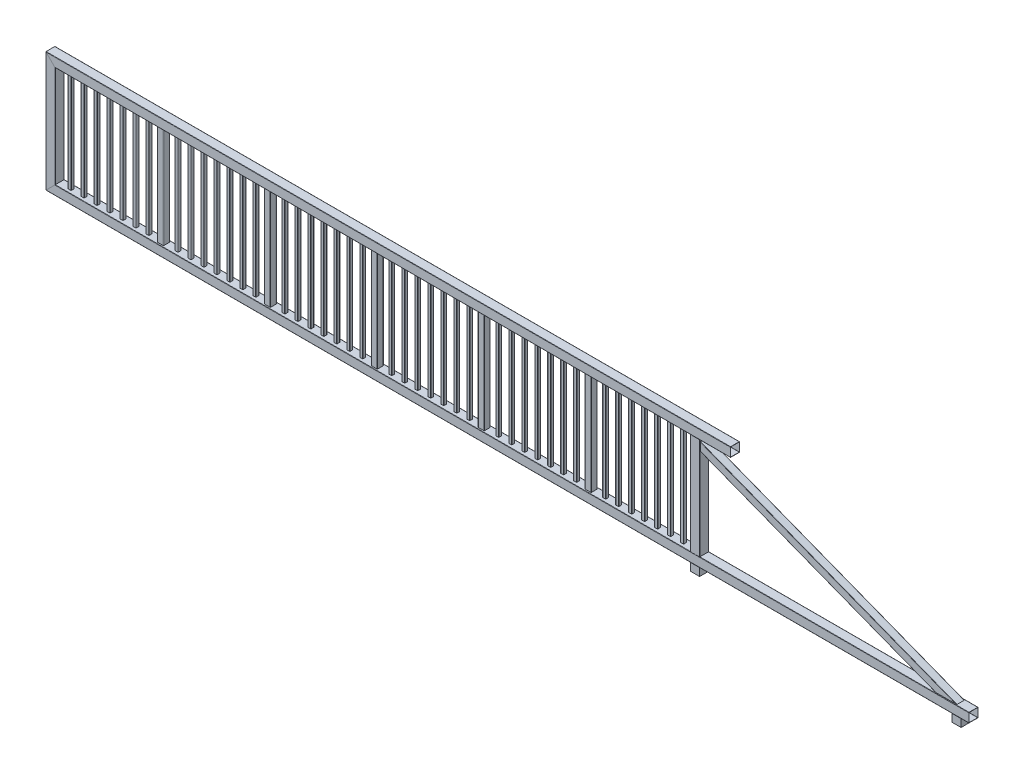
SolidWorks part; units mm, degrees
material "1.0037 (S235JR)"
ref_plane "Ebene vorne" through (0, 0, 0) normal (0, 0, 1) x (1, 0, 0)
ref_plane "Ebene oben" through (0, 0, 0) normal (0, 1, 0) x (1, 0, 0)
ref_plane "Ebene rechts" through (0, 0, 0) normal (1, 0, 0) x (0, 0, -1)
sketch "Skizze1" plane through (0, 0, 0) normal (0, 0, 1) x (1, 0, 0)
  line L0 (0, 0) -> (0, 1440)
  line L1 (0, 1440) -> (8840, 1440)
  line L2 (8380, 1320) -> (11790, 0)
  line L3 (11940, 0) -> (0, 0)
  line L4 (1410, 1440) -> (1410, 0)
  line L5 (2800, 1440) -> (2800, 0)
  line L6 (4190, 1440) -> (4190, 0)
  line L7 (5580, 1440) -> (5580, 0)
  line L8 (6970, 1440) -> (6970, 0)
  line L9 (5580, 1440) -> (5580, 0)
  line L10 (6970, 1440) -> (6970, 0)
  line L11 (1410, 864.301) -> (2800, 864.301) construction
  line L12 (2800, 864.301) -> (4190, 864.301) construction
  line L13 (4190, 864.301) -> (5580, 864.301) construction
  line L14 (5580, 864.301) -> (6970, 864.301) construction
  line L15 (6970, 864.301) -> (5580, 864.301) construction
  line L16 (5580, 864.301) -> (6970, 864.301) construction
  line L17 (8380, 1440) -> (8380, 0)
  line L18 (208.75, 1380) -> (208.75, 60)
  line L19 (60, 1380) -> (1370, 1380) construction
  line L20 (60, 1380) -> (60, 60) construction
  line L21 (60, 60) -> (1370, 60) construction
  line L22 (1370, 1380) -> (1370, 60) construction
  dimension "D1" = 8380
  dimension "D2" = 1440
  dimension "D3" = 460
  dimension "D4" = 1410
  dimension "D5" = 1390
  dimension "D6" = 11940
  dimension "D7" = 120
  dimension "D8" = 150
  dimension "D9" = 60
  dimension "D10" = 60
  dimension "D11" = 60
  dimension "D12" = 40
  dimension "D13" = 148.75
other "Strukturbauteil1"
ref_plane "Ebene1" through (0, 1440, 0) normal (1, 0, 0) x (0, 1, 0)
sketch "Skizze13" plane through (0, 1440, 0) normal (1, 0, 0) x (0, 1, 0)
  line L0 (57, -56) -> (57, 56)
  line L1 (56, -60) -> (-56, -60)
  line L2 (60, -56) -> (60, 56)
  line L3 (56, 60) -> (-56, 60)
  line L4 (-60, -56) -> (-60, 56)
  line L5 (56, 57) -> (-56, 57)
  line L6 (-57, -56) -> (-57, 56)
  line L7 (56, -57) -> (-56, -57)
  line L8 (0, -60) -> (0, 60) construction
  arc A0 (-60, 56) -> (-56, 60) centre (-56, 56) cw
  arc A1 (-56, -60) -> (-60, -56) centre (-56, -56) cw
  arc A2 (60, -56) -> (56, -60) centre (56, -56) cw
  arc A3 (56, 60) -> (60, 56) centre (56, 56) cw
  arc A4 (56, 57) -> (57, 56) centre (56, 56) cw
  arc A5 (-57, 56) -> (-56, 57) centre (-56, 56) cw
  arc A6 (-56, -57) -> (-57, -56) centre (-56, -56) cw
  arc A7 (57, -56) -> (56, -57) centre (56, -56) cw
  point P4 (0, 60)
  point P5 (0, -60)
  point P10 (-60, -60)
  point P13 (60, -60)
  point P16 (60, 60)
  point P25 (-60, -60)
  point P26 (-60, 60)
  point P27 (60, 60)
  point P30 (60, -60)
  point P31 (0, 0)
  point P32 (-60, 0)
  point P33 (60, 0)
  point P34 (0, 0)
  dimension "D3" = 4
  dimension "D1" = 120
  dimension "D2" = 120
  dimension "D4" = 3
other "Strukturbauteil2"
ref_plane "Ebene2" through (1410, 1440, 0) normal (0, -1, 0) x (1, 0, 0)
sketch "Skizze14" plane through (1410, 1440, 0) normal (0, -1, 0) x (1, 0, 0)
  line L0 (37, -36) -> (37, 36)
  line L1 (36, -40) -> (-36, -40)
  line L2 (40, -36) -> (40, 36)
  line L3 (36, 40) -> (-36, 40)
  line L4 (-40, -36) -> (-40, 36)
  line L5 (36, 37) -> (-36, 37)
  line L6 (-37, -36) -> (-37, 36)
  line L7 (36, -37) -> (-36, -37)
  line L8 (0, -40) -> (0, 40) construction
  arc A0 (-40, 36) -> (-36, 40) centre (-36, 36) cw
  arc A1 (-36, -40) -> (-40, -36) centre (-36, -36) cw
  arc A2 (40, -36) -> (36, -40) centre (36, -36) cw
  arc A3 (36, 40) -> (40, 36) centre (36, 36) cw
  arc A4 (36, 37) -> (37, 36) centre (36, 36) cw
  arc A5 (-37, 36) -> (-36, 37) centre (-36, 36) cw
  arc A6 (-36, -37) -> (-37, -36) centre (-36, -36) cw
  arc A7 (37, -36) -> (36, -37) centre (36, -36) cw
  point P4 (0, 40)
  point P5 (0, -40)
  point P10 (-40, -40)
  point P13 (40, -40)
  point P16 (40, 40)
  point P25 (-40, -40)
  point P26 (-40, 40)
  point P27 (40, 40)
  point P30 (40, -40)
  point P31 (0, 0)
  point P32 (-40, 0)
  point P33 (40, 0)
  point P34 (0, 0)
  dimension "D3" = 4
  dimension "D1" = 80
  dimension "D2" = 80
  dimension "D4" = 3
ref_plane "Ebene3" through (-60, 0, 0) normal (-1, 0, 0) x (0, 0, 1)
other "Strukturbauteil3"
ref_plane "Ebene4" through (8380, 1320, 0) normal (0.9326, -0.361, 0) x (0.361, 0.9326, 0)
sketch "Skizze16" plane through (8380, 1320, 0) normal (0.9326, -0.361, 0) x (0.361, 0.9326, 0)
  line L0 (47, -46) -> (47, 46)
  line L1 (46, -50) -> (-46, -50)
  line L2 (50, -46) -> (50, 46)
  line L3 (46, 50) -> (-46, 50)
  line L4 (-50, -46) -> (-50, 46)
  line L5 (46, 47) -> (-46, 47)
  line L6 (-47, -46) -> (-47, 46)
  line L7 (46, -47) -> (-46, -47)
  line L8 (0, -50) -> (0, 50) construction
  arc A0 (-50, 46) -> (-46, 50) centre (-46, 46) cw
  arc A1 (-46, -50) -> (-50, -46) centre (-46, -46) cw
  arc A2 (50, -46) -> (46, -50) centre (46, -46) cw
  arc A3 (46, 50) -> (50, 46) centre (46, 46) cw
  arc A4 (46, 47) -> (47, 46) centre (46, 46) cw
  arc A5 (-47, 46) -> (-46, 47) centre (-46, 46) cw
  arc A6 (-46, -47) -> (-47, -46) centre (-46, -46) cw
  arc A7 (47, -46) -> (46, -47) centre (46, -46) cw
  point P4 (0, 50)
  point P5 (0, -50)
  point P10 (-50, -50)
  point P13 (50, -50)
  point P16 (50, 50)
  point P25 (-50, -50)
  point P26 (-50, 50)
  point P27 (50, 50)
  point P30 (50, -50)
  point P31 (0, 0)
  point P32 (-50, 0)
  point P33 (50, 0)
  point P34 (0, 0)
  dimension "D3" = 4
  dimension "D1" = 100
  dimension "D2" = 100
  dimension "D4" = 3
sketch "Skizze17" plane through (8840, 0, 0) normal (1, 0, 0) x (0, 0, -1)
  line L1 (-48.0534, 1380) -> (49.2378, 1380)
  line L2 (-48.0534, 1380) -> (-48.0534, 1446.1886)
  line L3 (-48.0534, 1446.1886) -> (49.2378, 1446.1886)
  line L4 (49.2378, 1380) -> (49.2378, 1446.1886)
  line L6 (-52.676, 60) -> (52.9402, 60)
  line L7 (-52.676, 60) -> (-52.676, -50.5438)
  line L8 (-52.676, -50.5438) -> (52.9402, -50.5438)
  line L9 (52.9402, 60) -> (52.9402, -50.5438)
  line L12 (-56, 1380) -> (56, 1380) construction
  line L13 (-56, 1380) -> (56, 1380) construction
  line L14 (-56, 60) -> (56, 60) construction
extrude "Schnitt-Linear austragen1" cut sketch "Skizze17" against normal through all and the other way through all contours L8 L9 L6 L7 | L4 L3 L2 L1
other "Strukturbauteil4"
ref_plane "Ebene5" through (208.75, 1380, 0) normal (0, -1, 0) x (1, 0, 0)
sketch "Skizze19" plane through (208.75, 1380, 0) normal (0, -1, 0) x (1, 0, 0)
  line L0 (17.5, -16.5) -> (17.5, 16.5)
  line L1 (16.5, -20) -> (-16.5, -20)
  line L2 (20, -16.5) -> (20, 16.5)
  line L3 (16.5, 20) -> (-16.5, 20)
  line L4 (-20, -16.5) -> (-20, 16.5)
  line L5 (16.5, 17.5) -> (-16.5, 17.5)
  line L6 (-17.5, -16.5) -> (-17.5, 16.5)
  line L7 (16.5, -17.5) -> (-16.5, -17.5)
  line L8 (0, -20) -> (0, 20) construction
  arc A0 (-20, 16.5) -> (-16.5, 20) centre (-16.5, 16.5) cw
  arc A1 (-16.5, -20) -> (-20, -16.5) centre (-16.5, -16.5) cw
  arc A2 (20, -16.5) -> (16.5, -20) centre (16.5, -16.5) cw
  arc A3 (16.5, 20) -> (20, 16.5) centre (16.5, 16.5) cw
  arc A4 (16.5, 17.5) -> (17.5, 16.5) centre (16.5, 16.5) cw
  arc A5 (-17.5, 16.5) -> (-16.5, 17.5) centre (-16.5, 16.5) cw
  arc A6 (-16.5, -17.5) -> (-17.5, -16.5) centre (-16.5, -16.5) cw
  arc A7 (17.5, -16.5) -> (16.5, -17.5) centre (16.5, -16.5) cw
  point P4 (0, 20)
  point P5 (0, -20)
  point P10 (-20, -20)
  point P13 (20, -20)
  point P16 (20, 20)
  point P25 (-20, -20)
  point P26 (-20, 20)
  point P27 (20, 20)
  point P30 (20, -20)
  point P31 (0, 0)
  point P32 (-20, 0)
  point P33 (20, 0)
  point P34 (0, 0)
  dimension "D3" = 3.5
  dimension "D1" = 40
  dimension "D2" = 40
  dimension "D4" = 2.5
pattern_linear "Lineares Muster1" count 7 spacing 168.75 along (1, 0, 0) of bodies 126
pattern_linear "Lineares Muster2" count 6 spacing 1390 along (1, 0, 0) of bodies 132 131 130 129 128 127 126
sketch "Skizze27" plane through (0, 0, 60) normal (0, 0, 1) x (1, 0, 0)
  line L0 (8440, 60) -> (8440, 1380) construction
  line L1 (8440, 1462.9351) -> (8288.6077, 1462.9351)
  line L2 (8440, 1462.9351) -> (8440, 1209.4123)
  line L3 (8440, 1209.4123) -> (8288.6077, 1209.4123)
  line L4 (8288.6077, 1462.9351) -> (8288.6077, 1209.4123)
extrude "Schnitt-Linear austragen2" cut sketch "Skizze27" against normal through all
sketch "Skizze28" plane through (0, -60, 0) normal (0, -1, 0) x (-1, 0, 0)
  line L1 (-8320, -60) -> (-8440, -60)
  line L2 (-8320, -60) -> (-8320, 60)
  line L3 (-8320, 60) -> (-8440, 60)
  line L4 (-8440, -60) -> (-8440, 60)
  line L6 (56, -60) -> (-11940, -60) construction
  line L7 (-11840, -60) -> (-11720, -60)
  line L8 (-11840, -60) -> (-11840, 60)
  line L9 (-11840, 60) -> (-11720, 60)
  line L10 (-11720, -60) -> (-11720, 60)
  line L11 (-11940, 56) -> (-11940, -56) construction
  line L12 (56, 60) -> (-11940, 60) construction
  line L13 (-8320, -56) -> (-8320, 56) construction
  dimension "D1" = 120
  dimension "D2" = 120
  dimension "D3" = 120
  dimension "D4" = 100
extrude "Aufsatz-Linear austragen1" add sketch "Skizze28" along normal blind 100 separate body
